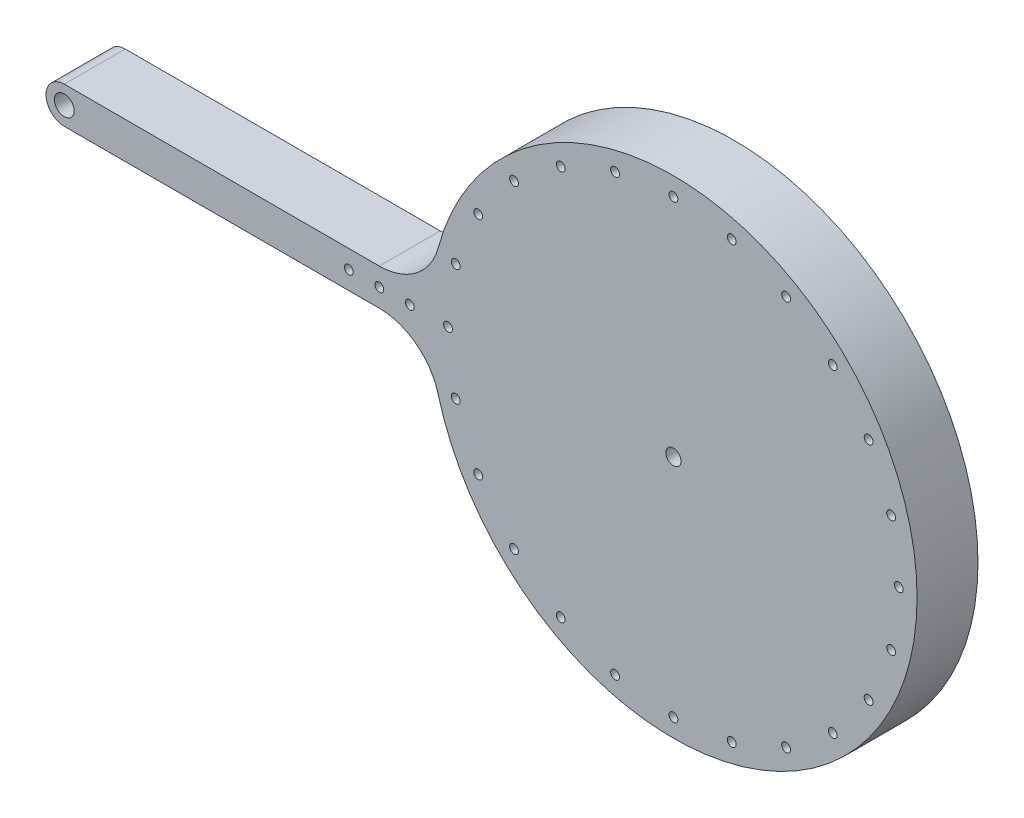
SolidWorks part; units mm, degrees
ref_plane "Front Plane" through (0, 0, 0) normal (0, 0, 1) x (1, 0, 0)
ref_plane "Top Plane" through (0, 0, 0) normal (0, 1, 0) x (1, 0, 0)
ref_plane "Right Plane" through (0, 0, 0) normal (1, 0, 0) x (0, 0, -1)
sketch "Sketch1" plane through (0, 0, 0) normal (0, 0, 1) x (1, 0, 0)
  line L0 (-155.3529, 10.2117) -> (-51.9137, 10.2117)
  line L1 (-51.9137, 22.2117) -> (-51.9137, 10.2117) construction
  line L5 (-51.9137, 22.2117) -> (-155.3529, 22.2117)
  arc A0 (-32.6016, -4.5883) -> (-51.9137, 10.2117) centre (-51.9137, -9.7883) ccw
  circle A1 centre (-19.4388, -20.7883) radius 1.45
  circle A2 centre (-26.8314, -2.9409) radius 1.45
  arc A3 (-51.9137, 22.2117) -> (-32.6016, 37.0117) centre (-51.9137, 42.2117) ccw
  arc A4 (-155.3529, 22.2117) -> (-155.3529, 10.2117) centre (-155.3529, 16.2117) ccw
  circle A5 centre (-155.3529, 16.2117) radius 3.25
  circle A6 centre (-26.8314, 35.3643) radius 1.45
  circle A7 centre (-19.4388, 53.2117) radius 1.45
  circle A8 centre (-29.3529, 16.2117) radius 1.45
  circle A9 centre (-51.9137, 16.2117) radius 1.45
  circle A10 centre (-41.9137, 16.2117) radius 1.45
  circle A11 centre (-61.9137, 16.2117) radius 1.45
  circle A14 centre (116.1256, -2.9409) radius 1.45
  circle A15 centre (108.733, -20.7883) radius 1.45
  circle A16 centre (96.973, -36.1142) radius 1.45
  circle A17 centre (81.6471, -47.8742) radius 1.45
  circle A18 centre (63.7997, -55.2668) radius 1.45
  circle A19 centre (44.6471, -57.7883) radius 1.45
  circle A20 centre (25.4945, -55.2668) radius 1.45
  circle A21 centre (7.6471, -47.8742) radius 1.45
  circle A22 centre (-7.6788, -36.1142) radius 1.45
  arc A23 (124.5879, 13.1348) -> (-32.6016, 37.0117) centre (44.6471, 16.2117) ccw
  arc A24 (-32.6016, -4.5883) -> (124.5879, 13.1348) centre (44.6471, 16.2117) ccw
  circle A33 centre (44.6471, 16.2117) radius 2.5
  circle A34 centre (-7.6788, 68.5376) radius 1.45
  circle A35 centre (7.6471, 80.2976) radius 1.45
  circle A36 centre (25.4945, 87.6902) radius 1.45
  circle A37 centre (44.6471, 90.2117) radius 1.45
  circle A38 centre (63.7997, 87.6902) radius 1.45
  circle A39 centre (81.6471, 80.2976) radius 1.45
  circle A40 centre (96.973, 68.5376) radius 1.45
  circle A41 centre (108.733, 53.2117) radius 1.45
  circle A42 centre (116.1256, 35.3643) radius 1.45
  circle A44 centre (118.6471, 16.2117) radius 1.45
  dimension "D1" = 5
  dimension "D2" = 10
extrude "Boss-Extrude2" add sketch "Sketch1" along normal blind 20
